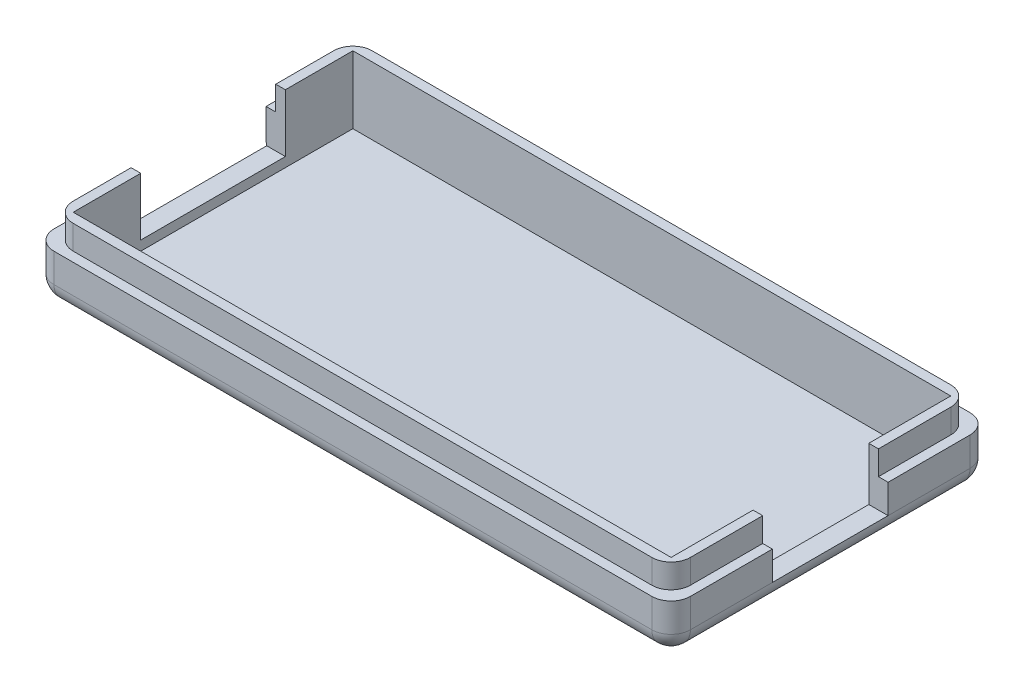
SolidWorks part; units mm, degrees
ref_plane "Front Plane" through (0, 0, 0) normal (0, 0, 1) x (1, 0, 0)
ref_plane "Top Plane" through (0, 0, 0) normal (0, 1, 0) x (1, 0, 0)
ref_plane "Right Plane" through (0, 0, 0) normal (1, 0, 0) x (0, 0, -1)
sketch "Sketch18" plane through (0, 0, 0) normal (1, 0, 0) x (0, 0, -1)
  line L0 (-618.0524, 198.0151) -> (-604.0905, 997.8933) construction
sketch "Sketch16" plane through (0, 0, 0) normal (0, 0, 1) x (1, 0, 0)
  line L0 (875.1222, -196.9214) -> (889.0841, -996.7996) construction
sketch "Sketch17" plane through (0, 0, 0) normal (0, 1, 0) x (1, 0, 0)
  line L0 (811.7508, -82.4927) -> (895.3736, -878.1102) construction
sketch "Sketch1" plane through (0, 0, 0) normal (0, 1, 0) x (1, 0, 0)
  line L1 (0, 0) -> (66, 0)
  line L2 (0, 0) -> (0, 33)
  line L3 (0, 33) -> (66, 33)
  line L4 (66, 0) -> (66, 33)
  dimension "D1" = 66
  dimension "D2" = 33
extrude "Boss-Extrude1" add sketch "Sketch1" along normal blind 5
sketch "Sketch2" plane through (0, 5, 0) normal (0, 1, 0) x (1, 0, 0)
  line L1 (1, 32) -> (65, 32)
  line L2 (1, 32) -> (1, 1)
  line L3 (1, 1) -> (65, 1)
  line L4 (65, 32) -> (65, 1)
  dimension "D1" = 64
  dimension "D2" = 31
  dimension "D3" = 1
  dimension "D4" = 1
extrude "Boss-Extrude2" add sketch "Sketch2" along normal blind 2.5
sketch "Sketch3" plane through (0, 7.5, 0) normal (0, 1, 0) x (1, 0, 0)
  line L1 (2, 31) -> (64, 31)
  line L2 (2, 31) -> (2, 2)
  line L3 (2, 2) -> (64, 2)
  line L4 (64, 31) -> (64, 2)
  dimension "D1" = 62
  dimension "D2" = 29
  dimension "D3" = 1
  dimension "D4" = 1
extrude "Cut-Extrude1" cut sketch "Sketch3" against normal blind 7
fillet "Fillet1" radius 2 8 edges at (0, 2.5, -33) (33, 0, -33) (66, 2.5, -33) (66, 0, -16.5) (66, 2.5, 0) (33, 0, 0) (0, 0, -16.5) (0, 2.5, 0)
fillet "Fillet2" radius 2 4 edges at (1, 6.25, -1) (1, 6.25, -32) (65, 6.25, -1) (65, 6.25, -32)
sketch "Sketch4" plane through (65, 0, 0) normal (1, 0, 0) x (0, 0, -1)
  line L0 (3, 7.5) -> (30, 7.5) construction
  line L1 (10.5, 7.5) -> (22.5, 7.5)
  line L2 (10.5, 7.5) -> (10.5, 5)
  line L3 (10.5, 5) -> (22.5, 5)
  line L4 (22.5, 7.5) -> (22.5, 5)
  line L5 (2, 5) -> (31, 5) construction
  dimension "D1" = 7.5
  dimension "D2" = 7.5
extrude "Cut-Extrude2" cut sketch "Sketch4" against normal blind 7
sketch "Sketch10" plane through (66, 0, 0) normal (1, 0, 0) x (0, 0, -1)
  line L0 (2, 5) -> (31, 5) construction
  line L1 (10.5, 5) -> (22.5, 5)
  line L2 (10.5, 5) -> (10.5, 2)
  line L3 (10.5, 2) -> (22.5, 2)
  line L4 (22.5, 5) -> (22.5, 2)
  line L5 (2, 2) -> (31, 2) construction
  dimension "D1" = 12
  dimension "D2" = 8.5
extrude "Cut-Extrude3" cut sketch "Sketch10" against normal blind 7
sketch "Sketch11" plane through (1, 0, 0) normal (-1, 0, 0) x (0, 0, 1)
  line L0 (-30, 7.5) -> (-3, 7.5) construction
  line L1 (-24, 7.5) -> (-9, 7.5)
  line L2 (-24, 7.5) -> (-24, 5)
  line L3 (-24, 5) -> (-9, 5)
  line L4 (-9, 7.5) -> (-9, 5)
  line L5 (-30, 5) -> (-3, 5) construction
  dimension "D1" = 15
  dimension "D2" = 6
extrude "Cut-Extrude4" cut sketch "Sketch11" against normal blind 7
sketch "Sketch12" plane through (0, 0, 0) normal (-1, 0, 0) x (0, 0, 1)
  line L0 (-31, 5) -> (-2, 5) construction
  line L1 (-24, 5) -> (-9, 5)
  line L2 (-24, 5) -> (-24, 1.5)
  line L3 (-24, 1.5) -> (-9, 1.5)
  line L4 (-9, 5) -> (-9, 1.5)
  dimension "D1" = 15
  dimension "D2" = 7
  dimension "D3" = 3.5
extrude "Cut-Extrude5" cut sketch "Sketch12" against normal blind 7
